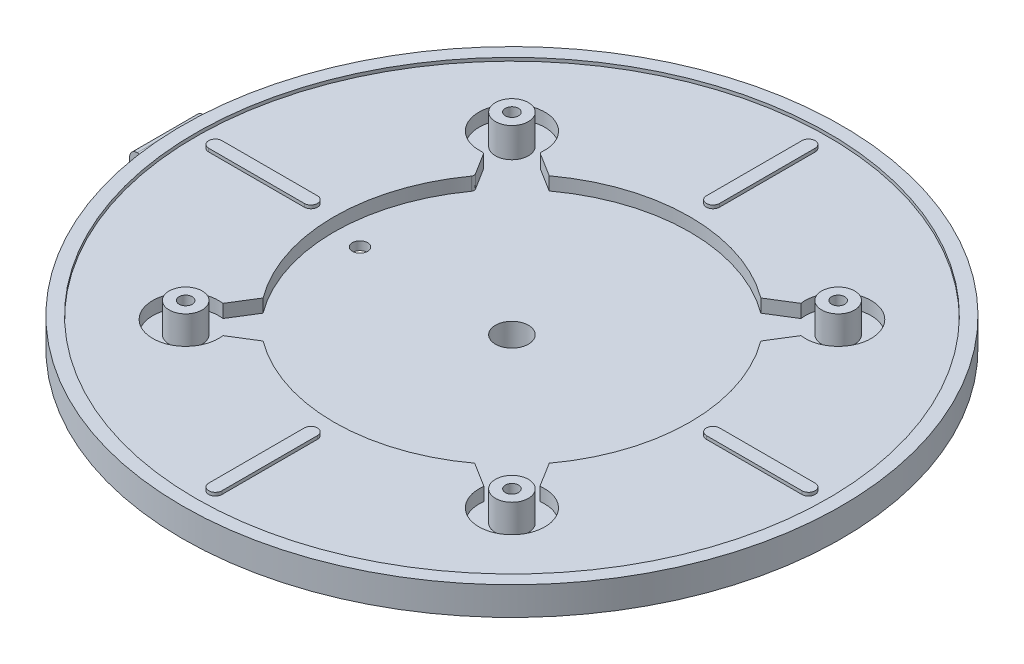
SolidWorks part; units mm, degrees
material "ABS"
ref_plane "Front Plane" through (0, 0, 0) normal (0, 0, 1) x (1, 0, 0)
ref_plane "Top Plane" through (0, 0, 0) normal (0, 1, 0) x (1, 0, 0)
ref_plane "Right Plane" through (0, 0, 0) normal (1, 0, 0) x (0, 0, -1)
sketch "Sketch1" plane through (0, 0, 0) normal (0, 1, 0) x (1, 0, 0)
  circle A0 centre (0, 0) radius 50
  dimension "D1" = 100
extrude "Boss-Extrude1" add sketch "Sketch1" along normal blind 4.3
sketch "Sketch3" plane through (0, 4.3, 0) normal (0, 1, 0) x (1, 0, 0)
  circle A0 centre (0, 0) radius 48
  dimension "D1" = 96
extrude "Cut-Extrude1" cut sketch "Sketch3" against normal blind 0.5
sketch "Sketch4" plane through (0, 3.8, 0) normal (0, 1, 0) x (1, 0, 0)
  line L0 (30.5, 0) -> (45, 0) construction
  line L1 (-2.365, 0) -> (2.365, 0) construction
  line L2 (30.5, 1) -> (45, 1)
  line L3 (30.5, -1) -> (45, -1)
  arc A0 (30.5, 1) -> (30.5, -1) centre (30.5, 0) ccw
  arc A1 (45, -1) -> (45, 1) centre (45, 0) ccw
  circle A3 centre (0, 0) radius 48 construction
  point P5 (37.75, 0)
  point P12 (46, 0)
  dimension "D1" = 16.5
  dimension "D3" = 2
  dimension "D2" = 2
extrude "Boss-Extrude2" add sketch "Sketch4" along normal blind 0.5
pattern_circular "CirPattern1" count 4 over 360 about axis through (0, 0, 0) along (0, 1, 0) of "Boss-Extrude2"
sketch "Sketch5" plane through (0, 3.8, 0) normal (0, 1, 0) x (1, 0, 0)
  line L4 (19.799, -24.0416) -> (16.0528, -21.7096)
  line L5 (21.7096, -16.0528) -> (24.0416, -19.799)
  line L6 (-24.0416, -19.799) -> (-21.7096, -16.0528)
  line L8 (-16.0528, -21.7096) -> (-19.799, -24.0416)
  line L9 (-19.5313, 23.875) -> (-16.0528, 21.7096)
  line L11 (-21.888, 16.3392) -> (-23.875, 19.5313)
  line L12 (24.0416, 19.799) -> (21.7096, 16.0528)
  line L14 (16.0528, 21.7096) -> (19.799, 24.0416)
  arc A0 (21.7096, -16.0528) -> (21.7096, 16.0528) centre (0, 0) ccw
  arc A1 (19.799, -24.0416) -> (24.0416, -19.799) centre (24.7487, -24.7487) ccw
  arc A2 (-24.0416, -19.799) -> (-19.799, -24.0416) centre (-24.7487, -24.7487) ccw
  arc A3 (-19.7654, 24.3403) -> (-24.3403, 19.7654) centre (-24.7487, 24.7487) ccw
  arc A4 (24.0416, 19.799) -> (19.799, 24.0416) centre (24.7487, 24.7487) ccw
  arc A5 (-16.0528, -21.7096) -> (16.0528, -21.7096) centre (0, 0) ccw
  arc A6 (-21.9067, 15.7827) -> (-21.7096, -16.0528) centre (0, 0) ccw
  arc A7 (16.0528, 21.7096) -> (-16.0528, 21.7096) centre (0, 0) ccw
  arc A8 (-21.888, 16.3392) -> (-21.9067, 15.7827) centre (-22.3124, 16.075) cw
  arc A9 (-23.875, 19.5313) -> (-24.3403, 19.7654) centre (-24.2995, 19.2671) ccw
  arc A10 (-19.7654, 24.3403) -> (-19.5313, 23.875) centre (-19.2671, 24.2995) ccw
  point P29 (0, 0)
  dimension "D1" = 54
  dimension "D3" = 10
  dimension "D2" = 0.5
  dimension "D4" = 35
  dimension "D5" = 6
  dimension "D6" = 4
  dimension "D7" = 8
extrude "Cut-Extrude2" cut sketch "Sketch5" against normal blind 2
sketch "Sketch6" plane through (0, 1.8, 0) normal (0, 1, 0) x (1, 0, 0)
  line L0 (0, 0) -> (24.7487, 24.7487)
  line L1 (0, -2.365) -> (0, 2.365) construction
  circle A0 centre (24.7487, 24.7487) radius 2.5
  dimension "D3" = 5
  dimension "D1" = 35
  dimension "D2" = 45
extrude "Boss-Extrude3" add sketch "Sketch6" along normal blind 4.5
pattern_circular "CirPattern2" count 4 over 360 about axis through (0, 0, 0) along (0, 1, 0) of "Boss-Extrude3"
sketch "Sketch7" plane through (0, 6.3, 0) normal (0, 1, 0) x (1, 0, 0)
  circle A1 centre (24.7487, 24.7487) radius 1
  point P0 (0, 0)
  point P1 (0, 0)
  dimension "D3" = 2
  dimension "D1" = 35
extrude "Cut-Extrude3" cut sketch "Sketch7" against normal through all
pattern_circular "CirPattern3" count 4 over 360 about axis through (0, 0, 0) along (0, 1, 0) of "Cut-Extrude3"
sketch "Sketch9" plane through (0, 0, 0) normal (0, -1, 0) x (1, 0, 0)
  circle A0 centre (0, 0) radius 49
  dimension "D1" = 98
extrude "Cut-Extrude5" cut sketch "Sketch9" against normal blind 0.5
sketch "Sketch10" plane through (0, 0.5, 0) normal (0, -1, 0) x (1, 0, 0)
  line L3 (-18.5751, 24.9895) -> (-16.4466, 23.4399)
  line L4 (-23.4399, 16.4466) -> (-24.9895, 18.5751)
  line L5 (24.9895, 18.5751) -> (23.4399, 16.4466)
  line L6 (16.4466, 23.4399) -> (18.5751, 24.9895)
  line L7 (18.5751, -24.9895) -> (16.4466, -23.4399)
  line L8 (23.4399, -16.4466) -> (24.9895, -18.5751)
  line L9 (-24.9895, -18.5751) -> (-23.4399, -16.4466)
  line L10 (-16.4466, -23.4399) -> (-18.5751, -24.9895)
  arc A0 (-23.4302, 15.8719) -> (-23.4302, -15.8719) centre (0, 0) ccw
  arc A1 (-18.7783, 25.3441) -> (-25.3441, 18.7783) centre (-24.7487, 24.7487) ccw
  arc A2 (-23.2319, 16.1608) -> (-23.2319, -16.1608) centre (0, 0) ccw
  arc A3 (25.3441, 18.7783) -> (18.7783, 25.3441) centre (24.7487, 24.7487) ccw
  arc A4 (-23.2319, 16.1608) -> (-23.2319, -16.1608) centre (0, 0) ccw
  arc A5 (18.7783, -25.3441) -> (25.3441, -18.7783) centre (24.7487, -24.7487) ccw
  arc A6 (-23.2319, 16.1608) -> (-23.2319, -16.1608) centre (0, 0) ccw
  arc A7 (-25.3441, -18.7783) -> (-18.7783, -25.3441) centre (-24.7487, -24.7487) ccw
  arc A8 (15.8719, 23.4302) -> (-15.8719, 23.4302) centre (0, 0) ccw
  arc A9 (16.1608, 23.2319) -> (-16.1608, 23.2319) centre (0, 0) ccw
  arc A10 (16.1608, 23.2319) -> (-16.1608, 23.2319) centre (0, 0) ccw
  arc A11 (16.1608, 23.2319) -> (-16.1608, 23.2319) centre (0, 0) ccw
  arc A12 (-15.8719, -23.4302) -> (15.8719, -23.4302) centre (0, 0) ccw
  arc A13 (-16.1608, -23.2319) -> (16.1608, -23.2319) centre (0, 0) ccw
  arc A14 (-16.1608, -23.2319) -> (16.1608, -23.2319) centre (0, 0) ccw
  arc A15 (-16.1608, -23.2319) -> (16.1608, -23.2319) centre (0, 0) ccw
  arc A16 (23.4302, -15.8719) -> (23.4302, 15.8719) centre (0, 0) ccw
  arc A17 (23.2319, -16.1608) -> (23.2319, 16.1608) centre (0, 0) ccw
  arc A18 (23.2319, -16.1608) -> (23.2319, 16.1608) centre (0, 0) ccw
  arc A19 (23.2319, -16.1608) -> (23.2319, 16.1608) centre (0, 0) ccw
  arc A20 (25.3441, 18.7783) -> (24.9895, 18.5751) centre (25.3937, 18.2808) ccw
  arc A21 (23.4399, 16.4466) -> (23.4302, 15.8719) centre (23.8441, 16.1523) ccw
  arc A22 (23.4399, -16.4466) -> (23.4302, -15.8719) centre (23.8441, -16.1523) cw
  arc A23 (24.9895, -18.5751) -> (25.3441, -18.7783) centre (25.3937, -18.2808) ccw
  arc A24 (18.5751, -24.9895) -> (18.7783, -25.3441) centre (18.2808, -25.3937) cw
  arc A25 (16.4466, -23.4399) -> (15.8719, -23.4302) centre (16.1523, -23.8441) ccw
  arc A26 (-15.8719, -23.4302) -> (-16.4466, -23.4399) centre (-16.1523, -23.8441) ccw
  arc A27 (-18.5751, -24.9895) -> (-18.7783, -25.3441) centre (-18.2808, -25.3937) ccw
  arc A28 (-25.3441, -18.7783) -> (-24.9895, -18.5751) centre (-25.3937, -18.2808) ccw
  arc A29 (-23.4399, -16.4466) -> (-23.4302, -15.8719) centre (-23.8441, -16.1523) ccw
  arc A30 (-23.4302, 15.8719) -> (-23.4399, 16.4466) centre (-23.8441, 16.1523) ccw
  arc A31 (-25.3441, 18.7783) -> (-24.9895, 18.5751) centre (-25.3937, 18.2808) cw
  arc A32 (-18.5751, 24.9895) -> (-18.7783, 25.3441) centre (-18.2808, 25.3937) cw
  arc A33 (-16.4466, 23.4399) -> (-15.8719, 23.4302) centre (-16.1523, 23.8441) ccw
  arc A34 (15.8719, 23.4302) -> (16.4466, 23.4399) centre (16.1523, 23.8441) ccw
  arc A35 (18.5751, 24.9895) -> (18.7783, 25.3441) centre (18.2808, 25.3937) ccw
  circle A36 centre (0, 0) radius 44.2616
  point P31 (0, 0)
  point P54 (-25.1245, 18.7605)
  point P57 (-18.7605, 25.1245)
  dimension "D1" = 56.6
  dimension "D2" = 12
  dimension "D6" = 0.5
  dimension "D3" = 9
  dimension "D4" = 4
  dimension "D5" = 10
extrude "Cut-Extrude10" cut sketch "Sketch10" against normal blind 1.8 contours A36 L6 A35 A3 A20 L5 A21 A16 A22 L8 A23 A5 A24 L7 A25 A12 A26 L10 A27 A7 A28 L9 A29 A0 A30 L4 A31 A1 A32 L3 A33 A8 A34
sketch "Sketch12" plane through (0, 0.5, 0) normal (0, -1, 0) x (1, 0, 0)
  circle A0 centre (0, 0) radius 18
  dimension "D1" = 36
extrude "Boss-Extrude4" add sketch "Sketch12" along normal blind 4.2
sketch "Sketch13" plane through (0, -3.7, 0) normal (0, -1, 0) x (1, 0, 0)
  circle A0 centre (0, 0) radius 2.5
  dimension "D1" = 5
extrude "Cut-Extrude11" cut sketch "Sketch13" against normal through all
sketch "Sketch14" plane through (0, 0, 0) normal (0, 0, 1) x (1, 0, 0)
  line L0 (50, 4.3) -> (-50, 4.3) construction
  line L1 (-51.85, 2.3) -> (-50, 2.3)
  line L2 (-50, 4.3) -> (-50, 0) construction
  line L3 (-50, 2.3) -> (-50, 0)
  line L4 (55, 0) -> (-55, 0) construction
  line L5 (-50, 0) -> (-50.2, 0)
  line L6 (-50.7, -0.5) -> (-50.7, -2.55)
  line L7 (-53, -2.55) -> (-53, 1.15)
  arc A0 (-53, -2.55) -> (-50.7, -2.55) centre (-51.85, -2.55) ccw
  arc A1 (-51.85, 2.3) -> (-53, 1.15) centre (-51.85, 1.15) ccw
  arc A2 (-50.7, -0.5) -> (-50.2, 0) centre (-50.2, -0.5) cw
  dimension "D1" = 2.3
  dimension "D2" = 2.3
  dimension "D4" = 6
  dimension "D7" = 0.5
  dimension "D3" = 2
  dimension "D5" = 0
  dimension "D6" = 3
extrude "Boss-Extrude5" add sketch "Sketch14" along normal blind 5 and the other way blind 5 separate body
sketch "Sketch15" plane through (-50, 0, 0) normal (1, 0, 0) x (0, 0, -1)
  line L1 (-5, 0) -> (5, 0)
  line L2 (-5, 0) -> (-5, 2.3)
  line L3 (-5, 2.3) -> (5, 2.3)
  line L4 (5, 0) -> (5, 2.3)
extrude "Boss-Extrude6" add sketch "Sketch15" along normal blind 1
sketch "Sketch16" plane through (0, 1.8, 0) normal (0, 1, 0) x (1, 0, 0)
  line L0 (-2.365, 0) -> (2.365, 0) construction
  circle A0 centre (-23.05, 0) radius 1.15
  circle A1 centre (0, 0) radius 50 construction
  dimension "D1" = 2.3
  dimension "D2" = 25.8
extrude "Cut-Extrude12" cut sketch "Sketch16" against normal through all
